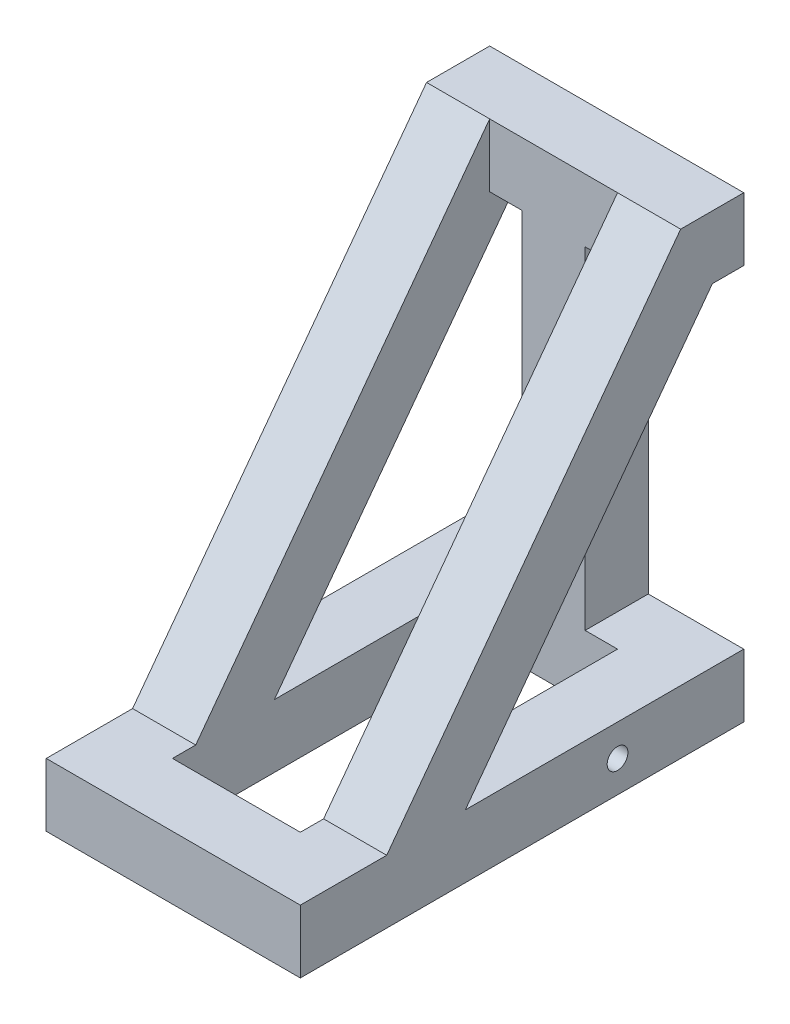
SolidWorks part; units mm, degrees
material "Pine"
ref_plane "Front Plane" through (0, 0, 0) normal (0, 0, 1) x (1, 0, 0)
ref_plane "Top Plane" through (0, 0, 0) normal (0, 1, 0) x (1, 0, 0)
ref_plane "Right Plane" through (0, 0, 0) normal (1, 0, 0) x (0, 0, -1)
sketch "Sketch1" plane through (0, 0, 0) normal (0, 1, 0) x (1, 0, 0)
  line L1 (-38.5, 95.5) -> (38.5, 95.5)
  line L2 (-38.5, 95.5) -> (-38.5, -95.5)
  line L3 (-38.5, -95.5) -> (38.5, -95.5)
  line L4 (38.5, 95.5) -> (38.5, -95.5)
  line L5 (0, -55) -> (0, 55) construction
  line L6 (-55, 0) -> (55, 0) construction
  line L7 (-76.5, 133.5) -> (76.5, 133.5)
  line L8 (76.5, 133.5) -> (76.5, -133.5)
  line L9 (-76.5, -133.5) -> (76.5, -133.5)
  line L10 (-76.5, 133.5) -> (-76.5, -133.5)
  dimension "D1" = 77
  dimension "D2" = 38.5
  dimension "D3" = 191
  dimension "D4" = 95.5
  dimension "D5" = 38
extrude "Boss-Extrude1" add sketch "Sketch1" along normal blind 38
sketch "Sketch2" plane through (0, 38, 0) normal (0, 1, 0) x (1, 0, 0)
  line L0 (76.5, 133.5) -> (-76.5, 133.5) construction
  line L1 (-19, 133.5) -> (19, 133.5)
  line L2 (-19, 133.5) -> (-19, 95.5)
  line L3 (-19, 95.5) -> (19, 95.5)
  line L4 (19, 133.5) -> (19, 95.5)
  line L5 (38.5, 95.5) -> (-38.5, 95.5) construction
  line L6 (0, -20.9) -> (0, 20.9) construction
  dimension "D1" = 38
  dimension "D2" = 19
extrude "Boss-Extrude2" add sketch "Sketch2" along normal blind 200
sketch "Sketch3" plane through (0, 0, 0) normal (1, 0, 0) x (0, 0, -1)
  line L1 (95.5, 238) -> (133.5, 238)
  line L2 (95.5, 238) -> (95.5, 276)
  line L3 (95.5, 276) -> (133.5, 276)
  line L4 (133.5, 238) -> (133.5, 276)
  dimension "D1" = 38
  dimension "D2" = 38
extrude "Boss-Extrude3" add sketch "Sketch3" along normal blind 76.5 and the other way blind 76.5
sketch "Sketch6" plane through (76.5, 0, 0) normal (1, 0, 0) x (0, 0, -1)
  line L0 (95.5, 276) -> (-81.5, 38)
  line L1 (-133.5, 38) -> (133.5, 38) construction
  line L2 (-81.5, 38) -> (-34.1433, 38)
  line L3 (-34.1433, 38) -> (114.5962, 238)
  line L4 (95.5, 238) -> (133.5, 238) construction
  line L5 (114.5962, 238) -> (95.5, 238)
  line L6 (95.5, 238) -> (95.5, 276)
  dimension "D1" = 38
  dimension "D2" = 52
extrude "Boss-Extrude4" add sketch "Sketch6" against normal blind 38
mirror "Mirror1" about plane through (0, 0, 0) normal (1, 0, 0) of "Boss-Extrude4"
sketch "Sketch7" plane through (76.5, 0, 0) normal (1, 0, 0) x (0, 0, -1)
  line L0 (-34.1433, 38) -> (133.5, 38) construction
  line L1 (133.5, 38) -> (133.5, 0) construction
  circle A0 centre (57.5, 19) radius 6.25
  dimension "D1" = 12.5
  dimension "D2" = 19
  dimension "D3" = 76
extrude "Cut-Extrude1" cut sketch "Sketch7" against normal through all
